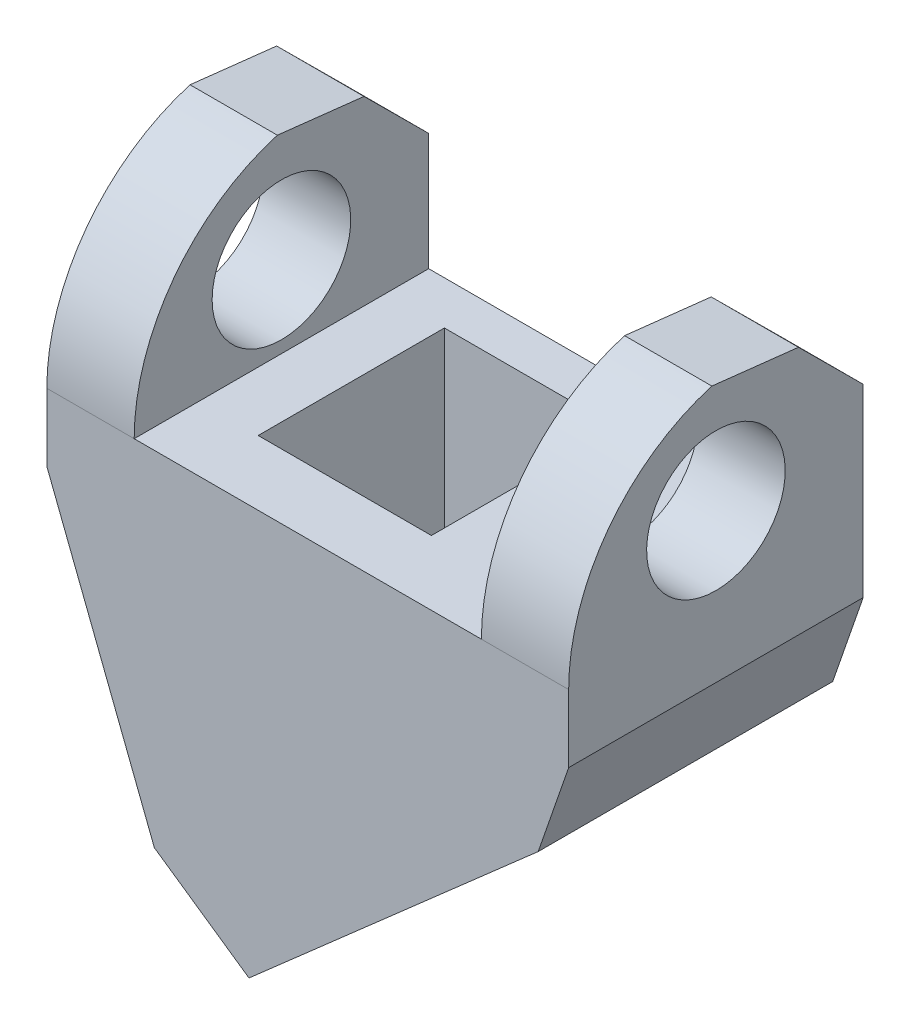
SolidWorks part; units mm, degrees
ref_plane "Ön Düzlem" through (0, 0, 0) normal (0, 0, 1) x (1, 0, 0)
ref_plane "Üst Düzlem" through (0, 0, 0) normal (0, 1, 0) x (1, 0, 0)
ref_plane "Sağ Düzlem" through (0, 0, 0) normal (1, 0, 0) x (0, 0, -1)
sketch "Sketch1" plane through (0, 0, 0) normal (0, 0, 1) x (1, 0, 0)
  line L0 (-30.544, 100.8614) -> (-25.502, 100.8614)
  line L1 (-25.502, 100.8614) -> (-25.502, 89.7634)
  line L2 (-25.502, 89.7634) -> (-5.4595, 89.7634)
  line L3 (-5.4595, 89.7634) -> (-5.4595, 100.8614)
  line L4 (-5.4595, 100.8614) -> (-0.4211, 100.8614)
  line L5 (-0.4211, 100.8614) -> (-0.4211, 85.8614)
  line L6 (-0.4211, 85.8614) -> (-2.1796, 80.7846)
  line L7 (-2.1796, 80.7846) -> (-18.8741, 66.1178)
  line L8 (-18.8741, 66.1178) -> (-24.337, 69.8995)
  line L9 (-24.337, 69.8995) -> (-30.544, 85.8614)
  line L10 (-30.544, 85.8614) -> (-30.544, 100.8614)
  dimension "D1" = 5.042
  dimension "D2" = 5.0383
  dimension "D4" = 15
  dimension "D6" = 5.3727
  dimension "D7" = 22.2221
  dimension "D8" = 6.6441
  dimension "D9" = 15.9619
  dimension "D10" = 158.751
  dimension "D11" = 145.943
  dimension "D12" = 104.006
extrude "Boss-Extrude1" add sketch "Sketch1" along normal blind 17
sketch "Sketch2" plane through (-25.502, 0, 0) normal (1, 0, 0) x (0, 0, -1)
  line L0 (0, 89.7634) -> (-17, 89.7634)
  line L1 (0, 89.7634) -> (0, 96.5274)
  line L2 (0, 96.5274) -> (-3.734, 100.2414)
  line L3 (-3.734, 100.2414) -> (-8.734, 100.8034)
  line L5 (-17, 89.7634) -> (-17, 100.8614) construction
  line L6 (-17, 89.7634) -> (-17, 100.8614)
  line L9 (-17, 100.8614) -> (0, 100.8614)
  line L10 (0, 100.8614) -> (0, 96.5274)
  arc A0 (-8.734, 100.8034) -> (-17, 89.7634) centre (-5.4945, 89.7634) ccw
  line M5 (0, 89.7634) -> (0, 100.8614)
  line M6 (0, 100.8614) -> (-17, 100.8614)
  line M7 (-17, 100.8614) -> (-17, 89.7634)
  dimension "D1" = 17
  dimension "D2" = 134.846
  dimension "D3" = 141.567
  dimension "D5" = 9.9953
  dimension "D6" = 6.764
  dimension "D7" = 5
extrude "Cut-Extrude1" cut sketch "Sketch2" against normal blind 15 and the other way blind 44 contours A0 L3 L2 M5 M6 M7
sketch "Sketch3" plane through (-41.0054, 46.6746, 0) normal (0.66, -0.7513, 0) x (0.7513, 0.66, 0)
  line L0 (33.4795, 17) -> (33.4795, 0) construction
  line L1 (29.459, 17) -> (51.6812, 17) construction
  line L2 (29.459, 0) -> (51.6812, 0) construction
  line L3 (33.4795, 0) -> (42.9531, 0) construction
  line L4 (42.9531, 0) -> (42.9531, 17) construction
  line L5 (42.9531, 17) -> (33.4795, 17) construction
  line L6 (33.4795, 13.2611) -> (33.4795, 2.5149)
  line L7 (33.4795, 2.5149) -> (42.9531, 2.5149)
  line L8 (42.9531, 2.5149) -> (42.9531, 13.2611)
  line L9 (42.9531, 13.2611) -> (33.4795, 13.2611)
  dimension "D1" = 4.0205
  dimension "D2" = 9.4736
  dimension "D3" = 10.7461
  dimension "D4" = 3.7389
ref_plane "Plane1" through (0, 0, 10) normal (0, 0, 1) x (1, 0, 0)
sketch "Sketch4" plane through (0, 0, 10) normal (0, 0, 1) x (1, 0, 0)
  line L0 (-14.8065, 69.6914) -> (-22.1166, 75.2189)
  line L1 (-15.8537, 68.7714) -> (-8.7366, 75.024) construction
  line L2 (-18.8741, 66.1178) -> (-2.1796, 80.7846) construction
sweep "Cut-Sweep1" cut profiles "Sketch3" path "Sketch4"
sketch "Sketch5" plane through (0, 89.7634, 0) normal (0, 1, 0) x (1, 0, 0)
  line L0 (-22.084, 0) -> (-22.084, -17) construction
  line L1 (-5.4595, 0) -> (-25.502, 0) construction
  line L2 (-5.4595, -17) -> (-25.502, -17) construction
  line L3 (-12.084, 0) -> (-12.084, -17) construction
  line L4 (-22.084, -2.51) -> (-12.084, -2.51)
  line L5 (-22.084, -13.26) -> (-12.084, -13.26)
  line L6 (-30.544, -8.734) -> (-30.544, -3.734) construction
  line L7 (-22.084, -2.51) -> (-22.084, -13.26)
  line L8 (-12.084, -2.51) -> (-12.084, -13.26)
  dimension "D1" = 8.46
  dimension "D2" = 3.74
  dimension "D3" = 10.75
  dimension "D4" = 10
extrude "Cut-Extrude4" cut sketch "Sketch5" against normal up to surface (23.8425 mm away)
ref_plane "Plane2" through (-15.4807, 0, 0) normal (-1, 0, 0) x (0, 0, 1)
sketch "Sketch6" plane through (-15.4807, 0, 0) normal (-1, 0, 0) x (0, 0, 1)
  line L0 (0, 85.8614) -> (17, 85.8614) construction
  line L1 (8.5, 85.8614) -> (8.5, 94.4593) construction
  circle A0 centre (8.5, 94.4593) radius 4
  dimension "D1" = 8.5979
  dimension "D2" = 8
extrude "Cut-Extrude5" cut sketch "Sketch6" against normal through all both and the other way through all
